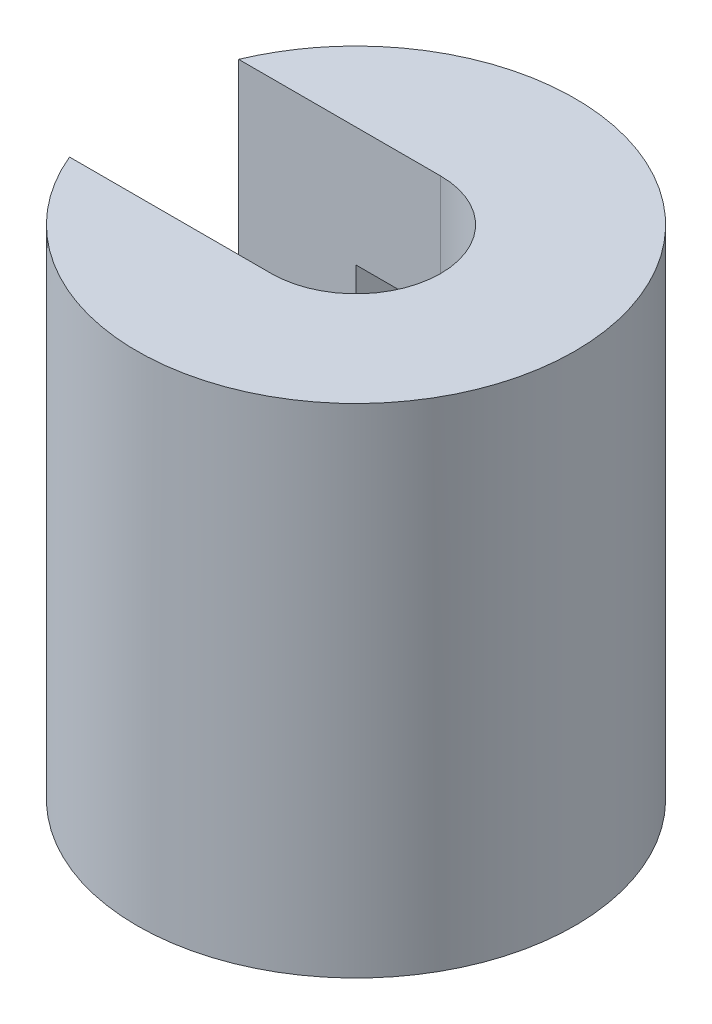
SolidWorks part; units mm, degrees
ref_plane "Alzado" through (0, 0, 0) normal (0, 0, 1) x (1, 0, 0)
ref_plane "Planta" through (0, 0, 0) normal (0, 1, 0) x (1, 0, 0)
ref_plane "Vista lateral" through (0, 0, 0) normal (1, 0, 0) x (0, 0, -1)
sketch "Croquis1" plane through (0, 0, 0) normal (0, 1, 0) x (1, 0, 0)
  circle A0 centre (0, 0) radius 11
  dimension "D2" = 22
extrude "Saliente-Extruir1" add sketch "Croquis1" along normal blind 25
sketch "Croquis2" plane through (0, 0, 0) normal (0, -1, 0) x (1, 0, 0)
  circle A0 centre (0, 0) radius 4.25
  dimension "D1" = 8.5
extrude "Cortar-Extruir1" cut sketch "Croquis2" against normal blind 5
sketch "Croquis3" plane through (0, 25, 0) normal (0, 1, 0) x (1, 0, 0)
  circle A0 centre (0, 0) radius 4.25
  dimension "D1" = 8.5
extrude "Cortar-Extruir2" cut sketch "Croquis3" against normal blind 6
sketch "Croquis5" plane through (0, 19, 0) normal (0, 1, 0) x (1, 0, 0)
  line L1 (4.25, 7.75) -> (-4.25, 7.75)
  line L2 (4.25, 7.75) -> (4.25, -7.75)
  line L3 (4.25, -7.75) -> (-4.25, -7.75)
  line L4 (-4.25, 7.75) -> (-4.25, -7.75)
  line L5 (4.25, 7.75) -> (-4.25, -7.75) construction
  line L6 (4.25, -7.75) -> (-4.25, 7.75) construction
  point P0 (0, 0)
  dimension "D1" = 8.5
  dimension "D2" = 15.5
extrude "Cortar-Extruir8" cut sketch "Croquis5" against normal blind 10
sketch "Croquis9" plane through (0, 0, 0) normal (1, 0, 0) x (0, 0, -1)
  line L0 (0, 0) -> (0, 9) construction
  line L1 (-7.75, 9) -> (7.75, 9)
  line L2 (-7.75, 9) -> (-7.75, 14.5)
  line L3 (-7.75, 14.5) -> (-4.25, 14.5)
  line L4 (7.75, 9) -> (7.75, 14.5)
  line L5 (-4.25, 14.5) -> (-4.25, 25.5)
  line L6 (-4.25, 25.5) -> (4.25, 25.5)
  line L7 (4.25, 25.5) -> (4.25, 14.5)
  line L8 (4.25, 14.5) -> (7.75, 14.5)
  line L9 (4.25, 14.5) -> (-4.25, 14.5) construction
  point P4 (0, 9)
  dimension "D1" = 9
  dimension "D2" = 15.5
  dimension "D3" = 5.5
  dimension "D4" = 8.5
  dimension "D5" = 11
extrude "Cortar-Extruir16" cut sketch "Croquis9" against normal through all
